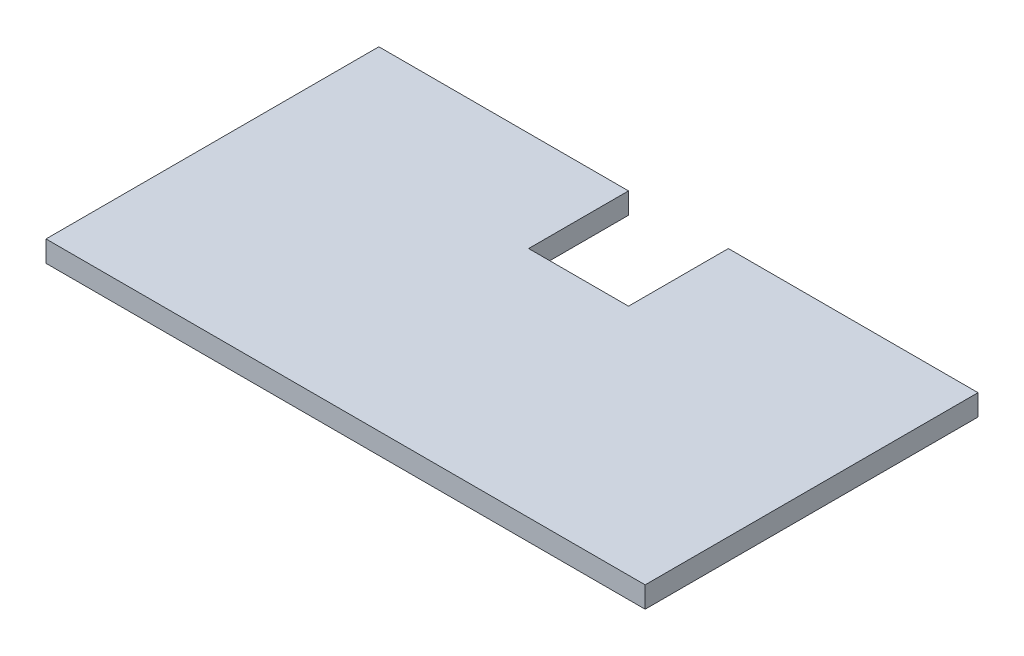
SolidWorks part; units mm, degrees
ref_plane "Front Plane" through (0, 0, 0) normal (0, 0, 1) x (1, 0, 0)
ref_plane "Top Plane" through (0, 0, 0) normal (0, 1, 0) x (1, 0, 0)
ref_plane "Right Plane" through (0, 0, 0) normal (1, 0, 0) x (0, 0, -1)
sketch "Sketch1" plane through (0, 0, 0) normal (0, 1, 0) x (1, 0, 0)
  line L1 (-45, 25) -> (45, 25)
  line L2 (-45, 25) -> (-45, -25)
  line L3 (-45, -25) -> (45, -25)
  line L4 (45, 25) -> (45, -25)
  line L5 (-45, 25) -> (45, -25) construction
  line L6 (-45, -25) -> (45, 25) construction
  point P0 (0, 0)
  dimension "D1" = 90
  dimension "D2" = 50
extrude "Boss-Extrude1" add sketch "Sketch1" along normal blind 3.175
sketch "Sketch2" plane through (0, 3.175, 0) normal (0, 1, 0) x (1, 0, 0)
  line L0 (45, 25) -> (-45, 25) construction
  line L1 (-7.5, 25) -> (7.5, 25)
  line L2 (-7.5, 25) -> (-7.5, 10)
  line L3 (-7.5, 10) -> (7.5, 10)
  line L4 (7.5, 25) -> (7.5, 10)
  point P6 (0, 10)
  dimension "D1" = 15
extrude "Cut-Extrude1" cut sketch "Sketch2" against normal through all
